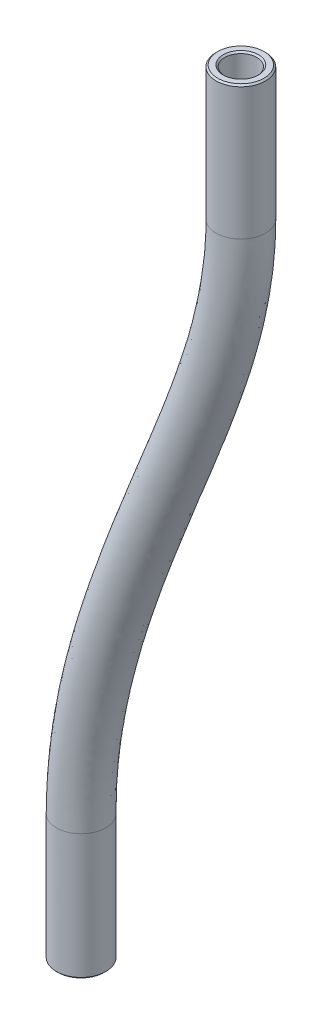
SolidWorks part; units mm, degrees
ref_plane "Front Plane" through (0, 0, 0) normal (0, 0, 1) x (1, 0, 0)
ref_plane "Top Plane" through (0, 0, 0) normal (0, 1, 0) x (1, 0, 0)
ref_plane "Right Plane" through (0, 0, 0) normal (1, 0, 0) x (0, 0, -1)
sketch3d "3DSketch1"
  line L0 (-150.0853, -93.2823, -25.525) -> (-150.0853, -103.4823, -25.525)
  line L1 (-138.6311, -35.8, -27.0016) -> (-138.6311, -46.6, -27.0016)
  spline S0 degree 3 poles (-138.6311, -46.6, -27.0016) (-138.6311, -53.4183, -27.0016) (-144.3582, -68.7915, -26.2633) (-150.0853, -83.9437, -25.525) (-150.0853, -93.2823, -25.525) knots 0 0 0 0 0.425349 1 1 1 1
sketch "Sketch1" plane through (0, -95.3823, 0) normal (0, 1, 0) x (1, 0, 0)
  circle A0 centre (-150.0853, 25.525) radius 2
  circle A1 centre (-150.0853, 25.525) radius 1.3
  circle A2 centre (-150.0853, 25.525) radius 2 construction
  dimension "D1" = 4
  dimension "D2" = 2.6
sweep "Sweep1" add profiles "Sketch1" path "3DSketch1"
chamfer "Chamfer1" distance 0.127 angle 45 4 edges at (-152.0853, -103.4823, -25.525) (-151.3853, -103.4823, -25.525) (-140.6311, -35.8, -27.0016) (-139.9311, -35.8, -27.0016)
